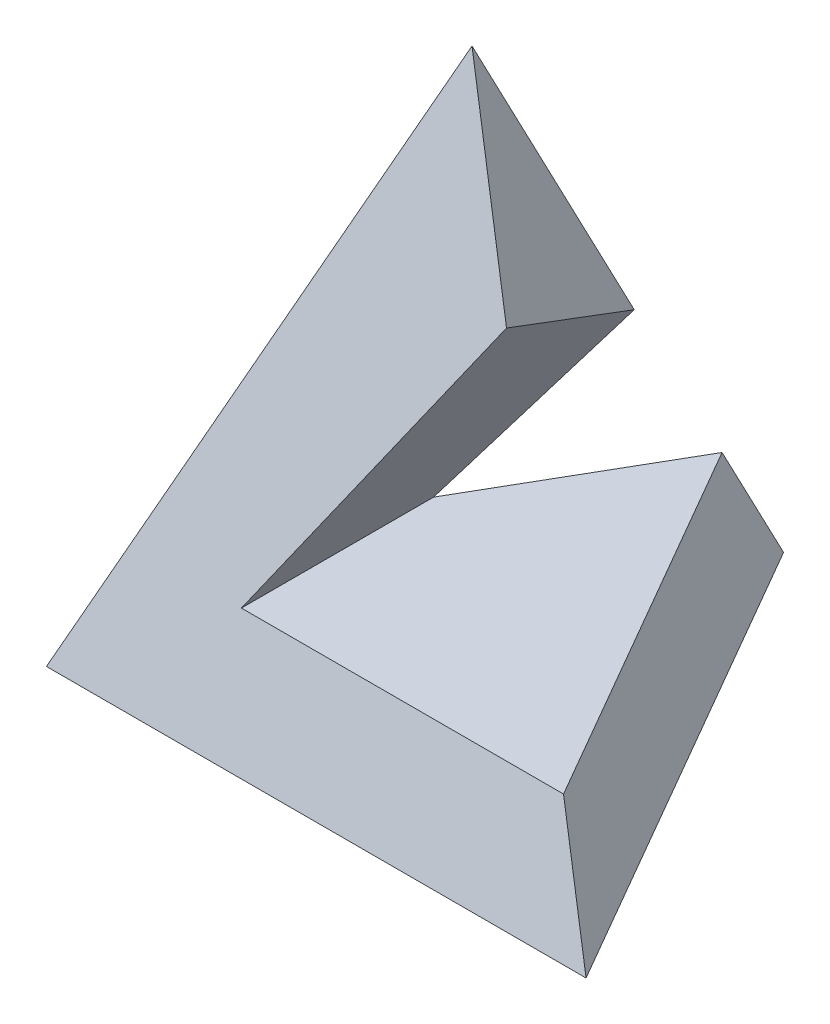
SolidWorks part; units mm, degrees
ref_plane "前视基准面" through (0, 0, 0) normal (0, 0, 1) x (1, 0, 0)
ref_plane "上视基准面" through (0, 0, 0) normal (0, 1, 0) x (1, 0, 0)
ref_plane "右视基准面" through (0, 0, 0) normal (1, 0, 0) x (0, 0, -1)
sketch "草图1" plane through (0, 0, 0) normal (0, 1, 0) x (1, 0, 0)
  line L1 (0, 39.8372) -> (-34.5, -19.9186)
  line L2 (-34.5, -19.9186) -> (34.5, -19.9186)
  line L3 (34.5, -19.9186) -> (0, 39.8372)
ref_plane "基准面4" through (0, 76, 0) normal (0, 1, 0) x (1, 0, 0)
sketch "草图9" plane through (0, 76, 0) normal (0, 1, 0) x (1, 0, 0)
  point P0 (0, 0)
loft "放样3" add profiles "草图9", "草图1"
ref_plane "基准面5" through (0, 15, 0) normal (0, 1, 0) x (1, 0, 0)
sketch "草图11" plane through (0, 0, 0) normal (0, 0, 1) x (1, 0, 0)
  line L0 (10.4408, 53) -> (27.6908, 15)
  line L1 (0, 76) -> (34.5, 0) construction
  line L2 (32.8658, 15) -> (-32.8658, 15) construction
  line L4 (27.6908, 15) -> (-13.5, 15)
  line L8 (10.4408, 53) -> (-13.5, 15)
extrude "切除-拉伸2" cut sketch "草图11" against normal mid plane 76 contours L8 L4 L0
